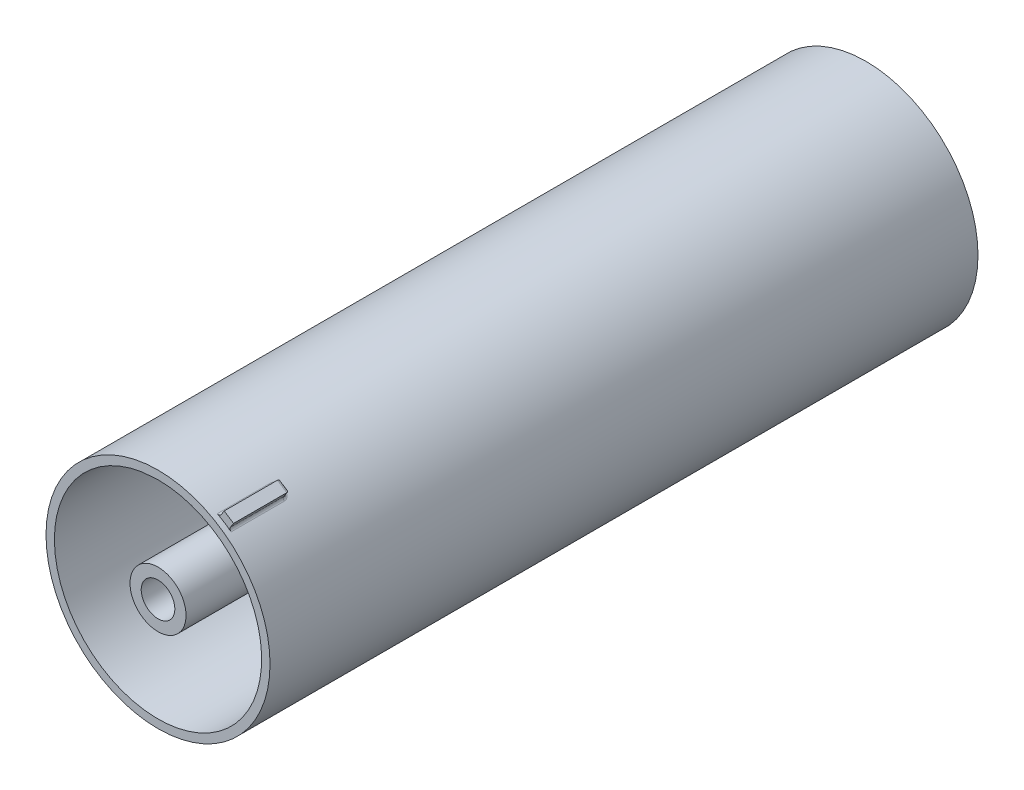
SolidWorks part; units mm, degrees
ref_plane "Спереди" through (0, 0, 0) normal (0, 0, 1) x (1, 0, 0)
ref_plane "Сверху" through (0, 0, 0) normal (0, 1, 0) x (1, 0, 0)
ref_plane "Справа" through (0, 0, 0) normal (1, 0, 0) x (0, 0, -1)
sketch "Эскиз2" plane through (0, 0, 0) normal (0, 0, 1) x (1, 0, 0)
  circle A0 centre (0, 0) radius 20
  circle A1 centre (0, 0) radius 18.5
  dimension "D1" = 40
  dimension "D2" = 37
extrude "Бобышка-Вытянуть1" add sketch "Эскиз2" along normal blind 126.4
sketch "Эскиз5" plane through (0, 0, 0) normal (0, 0, -1) x (-1, 0, 0)
  line L0 (0, 0) -> (0, 18.5) construction
  line L1 (0, 0) -> (2.9901, 18.2568) construction
  line L2 (0, 18.5) -> (0, 9.2195)
  line L3 (2.9901, 18.2568) -> (1.4901, 9.0983)
  circle A0 centre (0, 0) radius 18.5 construction
  arc A1 (0, 18.5) -> (2.9901, 18.2568) centre (0, 0) cw
  arc A2 (1.4901, 9.0983) -> (3.3687, 3.6948) centre (7.4112, 8.1286) ccw
  circle A3 centre (0, 0) radius 3
  arc A4 (-2.7273, 4.1907) -> (3.3687, 3.6948) centre (0, 0) ccw
  arc A5 (0, 9.2195) -> (-2.7273, 4.1907) centre (-6, 9.2195) cw
  point P16 (0, 5)
  dimension "D2" = 5
  dimension "D3" = 6
  dimension "D4" = 6
  dimension "D1" = 3
extrude "Бобышка-Вытянуть3" add sketch "Эскиз5" against normal through all
sketch "Sketch1" plane through (0, 0, 0) normal (0, 0, -1) x (-1, 0, 0)
  line L0 (0, 18.5) -> (2.9901, 18.2568)
  arc A2 (0, 18.5) -> (2.9901, 18.2568) centre (0, 0) ccw
  dimension "D1" = 18.5
extrude "Cut-Extrude1" cut sketch "Sketch1" against normal blind 59
sketch "Sketch2" plane through (0, 0, 126.4) normal (0, 0, 1) x (1, 0, 0)
  line L0 (0, 18.5) -> (-2.9901, 18.2568)
  arc A2 (0, 18.5) -> (-2.9901, 18.2568) centre (0, 0) cw
  dimension "D1" = 18.5
extrude "Cut-Extrude2" cut sketch "Sketch2" against normal blind 59
sketch "Sketch4" plane through (0, 0, 126.4) normal (0, 0, 1) x (1, 0, 0)
  line L0 (0, 0) -> (0, 18.5) construction
  line L1 (0, 18.5) -> (9.25, 16.0215) construction
  line L2 (9.25, 16.0215) -> (0, 0) construction
  line L3 (9.25, 16.0215) -> (10, 17.3205) construction
  line L4 (10, 17.3205) -> (11.6799, 16.2352)
  line L5 (10, 17.3205) -> (10.814, 18.5804)
  line L6 (10.814, 18.5804) -> (12.4939, 17.4951)
  line L7 (12.4939, 17.4951) -> (11.6799, 16.2352)
  circle A0 centre (0, 0) radius 18.5 construction
  circle A1 centre (0, 0) radius 20 construction
  arc A2 (10, 17.3205) -> (11.6799, 16.2352) centre (10.8399, 16.7778) cw construction
  dimension "D2" = 1
  dimension "D1" = 30
  dimension "D3" = 2
  dimension "D4" = 1.5
sketch "Sketch3" plane through (0, 0, 126.4) normal (0, 0, 1) x (1, 0, 0)
  circle A0 centre (0, 0) radius 5
  circle A1 centre (0, 0) radius 3
  dimension "D1" = 10
  dimension "D2" = 6
extrude "Boss-Extrude1" add sketch "Sketch3" against normal offset from surface (58.6 mm away) 0.4 separate body up to face at (-0.7247, 8.9083, 67.4)
extrude "Boss-Extrude2" add sketch "Sketch4" against normal blind 10 from offset 1 offset against normal yes
fillet "Fillet1" radius 0.5 6 edges at (11.6799, 16.2352, 120.4) (10, 17.3205, 120.4) (12.0869, 16.8651, 115.4) (11.654, 18.0377, 115.4) (10.407, 17.9505, 115.4) (10.8535, 16.7988, 115.4)
